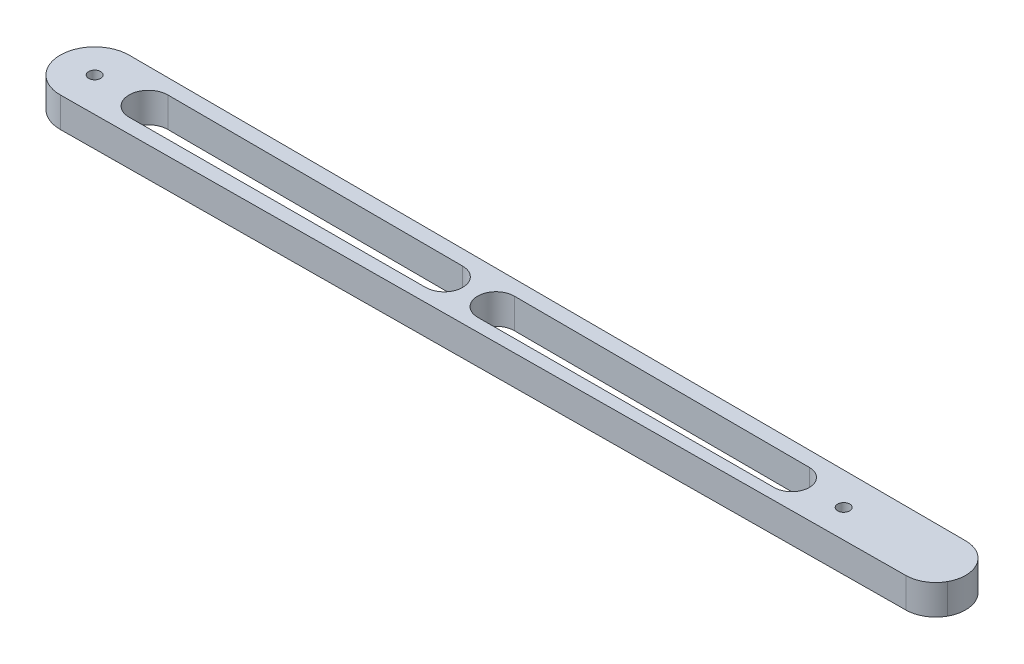
SolidWorks part; units mm, degrees
material "6061 Alloy"
ref_plane "Front Plane" through (0, 0, 0) normal (0, 0, 1) x (1, 0, 0)
ref_plane "Top Plane" through (0, 0, 0) normal (0, 1, 0) x (1, 0, 0)
ref_plane "Right Plane" through (0, 0, 0) normal (1, 0, 0) x (0, 0, -1)
sketch "Sketch1" plane through (0, 0, 0) normal (0, 1, 0) x (1, 0, 0)
  line L0 (0.0909, -11.4996) -> (280.0706, -9.2863)
  line L1 (280.0196, 10.7134) -> (0.0323, 11.5)
  arc A0 (0.0323, 11.5) -> (0.0909, -11.4996) centre (0, 0) ccw
  arc A1 (280.0706, -9.2863) -> (280.0196, 10.7134) centre (279.9915, 0.7134) ccw
  circle A2 centre (250, 0) radius 2
  circle A3 centre (0, 0) radius 2
  dimension "D1" = 23
  dimension "D3" = 20
  dimension "D4" = 4
  dimension "D6" = 4
  dimension "D5" = 250
  dimension "D7" = 30
extrude "Boss-Extrude1" add sketch "Sketch1" along normal blind 10
sketch "Sketch2" plane through (0, 10, 0) normal (0, 1, 0) x (1, 0, 0)
  line L0 (17.9677, 6.4495) -> (232.67, 5.8464) construction
  line L1 (17.9677, -6.4495) -> (232.67, -5.8464) construction
  line L2 (17.9496, 0) -> (116.6536, 0) construction
  line L3 (133.9496, 0) -> (232.6536, 0) construction
  line L4 (280.0196, 10.7134) -> (0.0323, 11.5) construction
  line L6 (17.9677, 6.4495) -> (116.671, 6.1722)
  line L7 (17.9677, -6.4495) -> (116.671, -6.1722)
  line L8 (133.9668, 6.1237) -> (232.67, 5.8464)
  line L9 (133.9668, -6.1237) -> (232.67, -5.8464)
  arc A0 (17.9677, 6.4495) -> (17.9677, -6.4495) centre (17.9496, 0) ccw
  arc A1 (116.671, -6.1722) -> (116.671, 6.1722) centre (116.6536, 0) ccw
  arc A2 (133.9668, 6.1237) -> (133.9668, -6.1237) centre (133.9496, 0) ccw
  arc A3 (232.67, -5.8464) -> (232.67, 5.8464) centre (232.6536, 0) ccw
  circle A7 centre (250, 0) radius 2 construction
  point P1 (11.5, 0)
  point P12 (238.5, 0)
  point P15 (122.8259, 0)
  point P17 (127.8259, 0)
  dimension "D1" = 11.5
  dimension "D4" = 5
  dimension "D2" = 5
  dimension "D3" = 11.5
extrude "Cut-Extrude1" cut sketch "Sketch2" against normal through all
sketch "Sketch3" plane through (0, 0, 0) normal (1, 0, 0) x (0, 0, -1)
  line L0 (-4.1103, 10) -> (-4.1103, 0)
  line L1 (10.7134, 10) -> (-9.2863, 10) construction
  line L2 (-9.2863, 0) -> (10.7134, 0) construction
split line "Split Line1"
